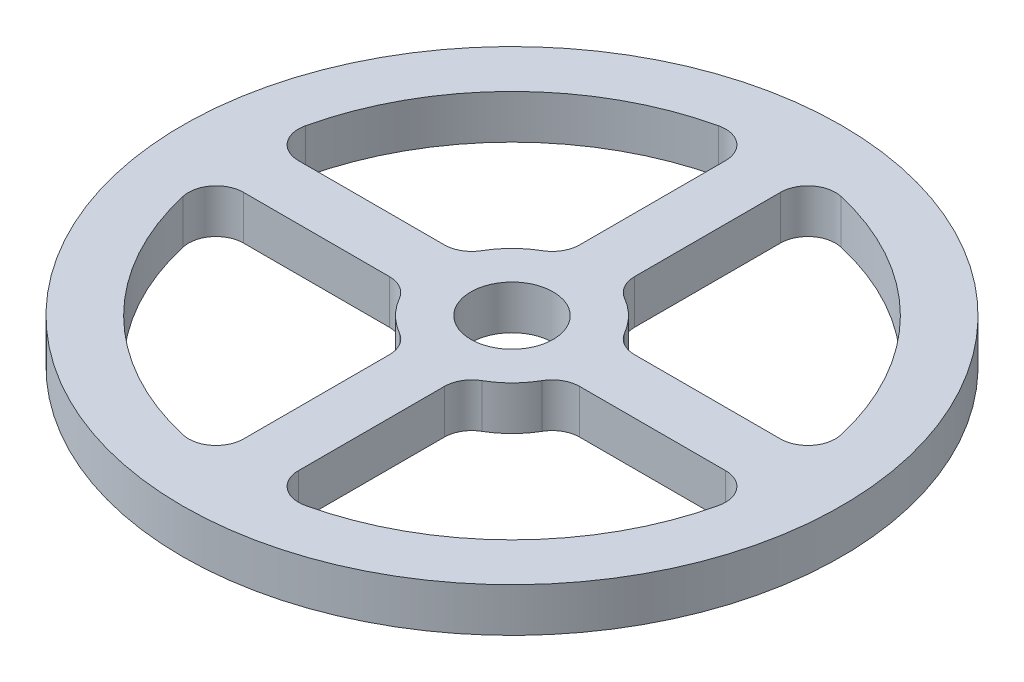
SolidWorks part; units mm, degrees
ref_plane "Front Plane" through (0, 0, 0) normal (0, 0, 1) x (1, 0, 0)
ref_plane "Top Plane" through (0, 0, 0) normal (0, 1, 0) x (1, 0, 0)
ref_plane "Right Plane" through (0, 0, 0) normal (1, 0, 0) x (0, 0, -1)
sketch "Sketch1" plane through (0, 0, 0) normal (0, 1, 0) x (1, 0, 0)
  line L0 (0, 0) -> (0, 139.4202) construction
  line L1 (0, 0) -> (155.583, 0) construction
  line L2 (34.641, 10) -> (87.7496, 10)
  line L3 (10, 34.641) -> (10, 87.7496)
  line L4 (-10, 34.641) -> (-10, 87.7496)
  line L5 (-34.641, 10) -> (-87.7496, 10)
  line L6 (34.641, -10) -> (87.7496, -10)
  line L7 (10, -34.641) -> (10, -87.7496)
  line L8 (-10, -34.641) -> (-10, -87.7496)
  line L9 (-34.641, -10) -> (-87.7496, -10)
  circle A0 centre (0, 0) radius 120
  arc A1 (-22.2222, 97.4996) -> (-97.4996, 22.2222) centre (0, 0) ccw
  arc A2 (-15, 25.9808) -> (-25.9808, 15) centre (0, 0) ccw
  circle A3 centre (0, 0) radius 15
  arc A4 (-97.4996, -22.2222) -> (-22.2222, -97.4996) centre (0, 0) ccw
  arc A5 (97.4996, 22.2222) -> (22.2222, 97.4996) centre (0, 0) ccw
  arc A6 (22.2222, -97.4996) -> (97.4996, -22.2222) centre (0, 0) ccw
  arc A7 (-25.9808, -15) -> (-15, -25.9808) centre (0, 0) ccw
  arc A8 (15, -25.9808) -> (25.9808, -15) centre (0, 0) ccw
  arc A9 (25.9808, 15) -> (15, 25.9808) centre (0, 0) ccw
  arc A10 (-87.7496, 10) -> (-97.4996, 22.2222) centre (-87.7496, 20) cw
  arc A11 (-87.7496, -10) -> (-97.4996, -22.2222) centre (-87.7496, -20) ccw
  arc A12 (-34.641, -10) -> (-25.9808, -15) centre (-34.641, -20) cw
  arc A13 (-34.641, 10) -> (-25.9808, 15) centre (-34.641, 20) ccw
  arc A14 (-10, 34.641) -> (-15, 25.9808) centre (-20, 34.641) cw
  arc A15 (10, 34.641) -> (15, 25.9808) centre (20, 34.641) ccw
  arc A16 (34.641, 10) -> (25.9808, 15) centre (34.641, 20) cw
  arc A17 (34.641, -10) -> (25.9808, -15) centre (34.641, -20) ccw
  arc A18 (10, -34.641) -> (15, -25.9808) centre (20, -34.641) cw
  arc A19 (-10, -34.641) -> (-15, -25.9808) centre (-20, -34.641) ccw
  arc A20 (-10, -87.7496) -> (-22.2222, -97.4996) centre (-20, -87.7496) cw
  arc A21 (10, -87.7496) -> (22.2222, -97.4996) centre (20, -87.7496) ccw
  arc A22 (87.7496, -10) -> (97.4996, -22.2222) centre (87.7496, -20) cw
  arc A23 (87.7496, 10) -> (97.4996, 22.2222) centre (87.7496, 20) ccw
  arc A24 (10, 87.7496) -> (22.2222, 97.4996) centre (20, 87.7496) cw
  arc A25 (-10, 87.7496) -> (-22.2222, 97.4996) centre (-20, 87.7496) ccw
  point P14 (11.038, 27.8956)
  point P15 (11.8264, 99.2982)
  point P28 (-99.4987, 10)
  point P31 (-99.4987, -10)
  point P34 (-28.2843, -10)
  point P37 (-28.2843, 10)
  point P40 (-10, 28.2843)
  point P43 (10, 28.2843)
  point P46 (28.2843, 10)
  point P49 (28.2843, -10)
  point P52 (10, -28.2843)
  point P55 (-10, -28.2843)
  point P58 (-10, -99.4987)
  point P61 (10, -99.4987)
  point P64 (99.4987, -10)
  point P67 (99.4987, 10)
  point P70 (10, 99.4987)
  point P73 (-10, 99.4987)
  dimension "D1" = 240
  dimension "D2" = 200
  dimension "D3" = 60
  dimension "D4" = 30
  dimension "D7" = 10
  dimension "D5" = 10
  dimension "D6" = 10
extrude "Boss-Extrude1" add sketch "Sketch1" along normal blind 16
